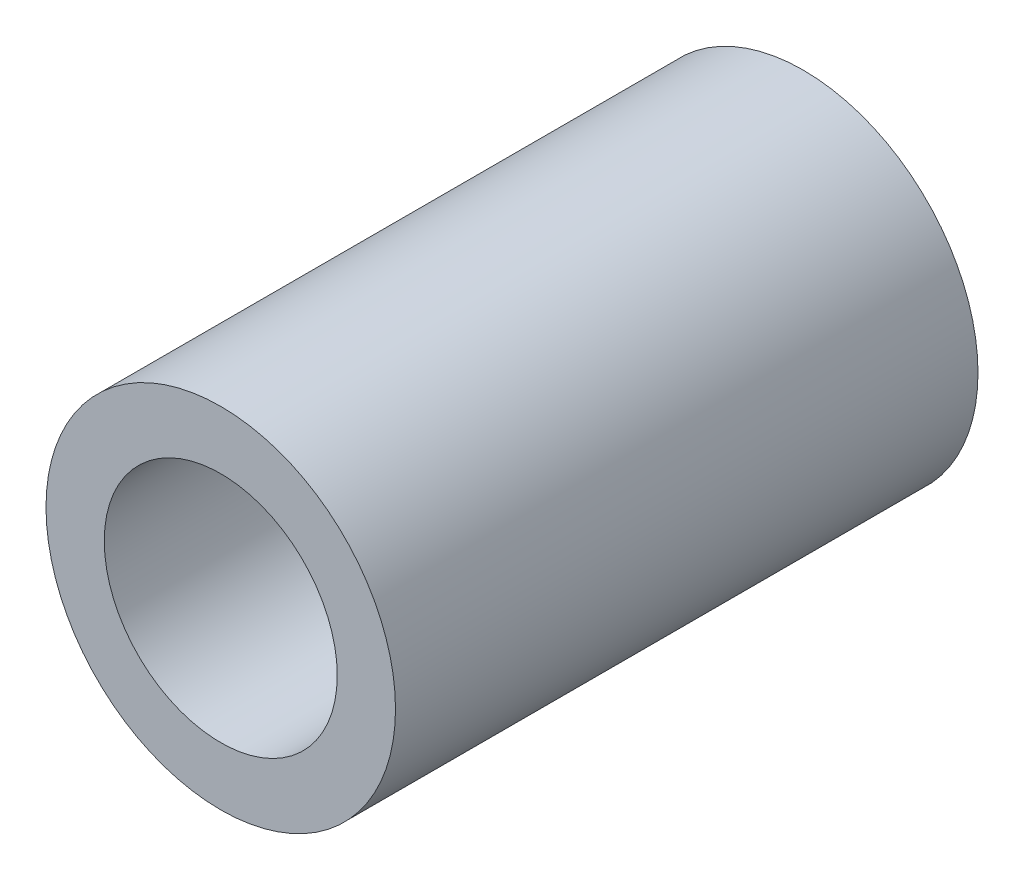
SolidWorks part; units mm, degrees
material "Alumina"
ref_plane "Front Plane" through (0, 0, 0) normal (0, 0, 1) x (1, 0, 0)
ref_plane "Top Plane" through (0, 0, 0) normal (0, 1, 0) x (1, 0, 0)
ref_plane "Right Plane" through (0, 0, 0) normal (1, 0, 0) x (0, 0, -1)
sketch "Sketch1" plane through (0, 0, 0) normal (0, 0, 1) x (1, 0, 0)
  circle A0 centre (0, -148.5737) radius 4.5
  circle A1 centre (0, 0) radius 4.5
  circle A2 centre (0, 0) radius 3
  dimension "D1" = 9
  dimension "D2" = 6
extrude "Boss-Extrude1" add sketch "Sketch1" along normal blind 15 contours A1 | A2
